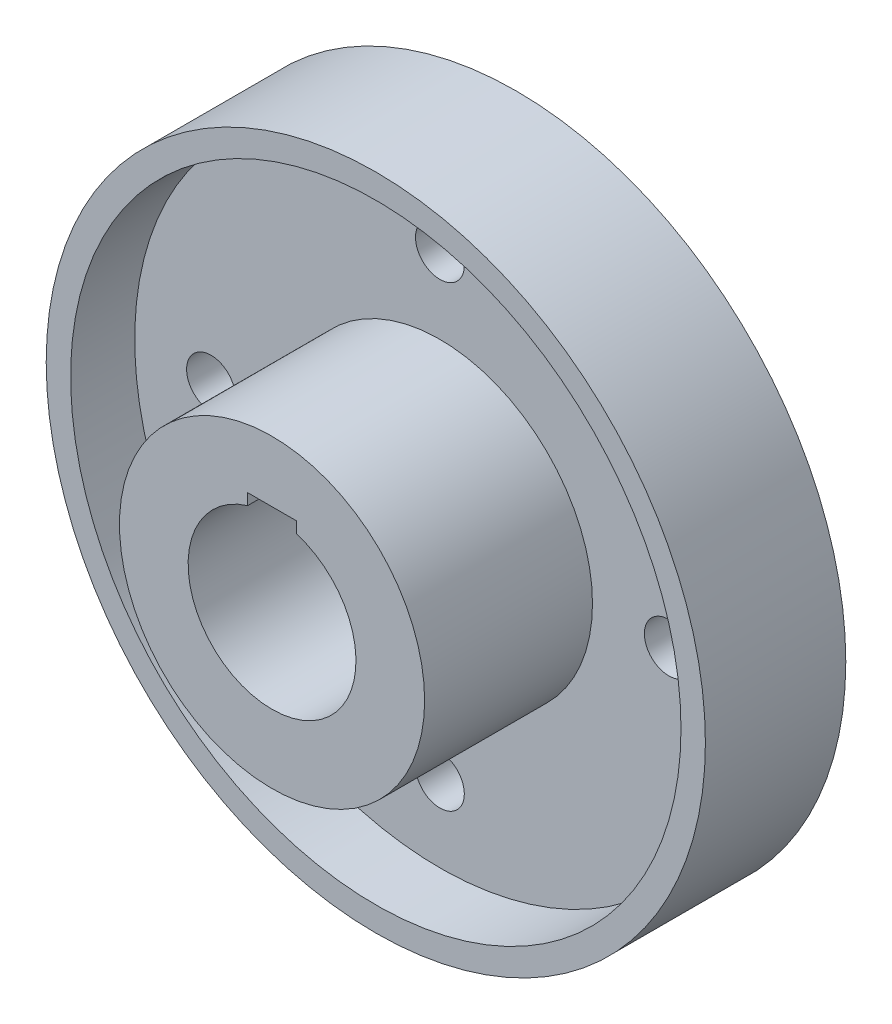
SolidWorks part; units mm, degrees
material "Gray Cast Iron"
ref_plane "Front Plane" through (0, 0, 0) normal (0, 0, 1) x (1, 0, 0)
ref_plane "Top Plane" through (0, 0, 0) normal (0, 1, 0) x (1, 0, 0)
ref_plane "Right Plane" through (0, 0, 0) normal (1, 0, 0) x (0, 0, -1)
sketch "Sketch1" plane through (0, 0, 0) normal (0, 0, 1) x (1, 0, 0)
  circle A0 centre (0, 0) radius 108
  dimension "D1" = 216
extrude "Boss-Extrude1" add sketch "Sketch1" along normal blind 25 contours A0
sketch "Sketch2" plane through (0, 0, 25) normal (0, 0, 1) x (1, 0, 0)
  circle A0 centre (0, 0) radius 108
  circle A1 centre (0, 0) radius 100
  dimension "D1" = 216
  dimension "D2" = 200
extrude "Boss-Extrude2" add sketch "Sketch2" along normal blind 21
sketch "Sketch3" plane through (0, 0, 25) normal (0, 0, 1) x (1, 0, 0)
  circle A0 centre (0, 0) radius 50
  circle A1 centre (0, 0) radius 27.5
  dimension "D1" = 100
  dimension "D2" = 55
extrude "Boss-Extrude3" add sketch "Sketch3" along normal blind 55
sketch "Sketch4" plane through (0, 0, 0) normal (0, 0, -1) x (-1, 0, 0)
  circle A0 centre (0, 0) radius 37.5
  dimension "D1" = 75
extrude "Boss-Extrude4" add sketch "Sketch4" along normal blind 5
sketch "Sketch6" plane through (0, 0, 25) normal (0, 0, 1) x (1, 0, 0)
  circle A0 centre (0, 0) radius 27.5
  dimension "D1" = 55
extrude "Cut-Extrude1" cut sketch "Sketch6" against normal through all
sketch "Sketch7" plane through (0, 0, 25) normal (0, 0, 1) x (1, 0, 0)
  line L0 (0, 0) -> (0, 75) construction
  circle A0 centre (0, 0) radius 75 construction
  circle A1 centre (0, 75) radius 8
  circle A2 centre (75, 0) radius 8
  circle A3 centre (0, -75) radius 8
  circle A4 centre (-75, 0) radius 8
  circle A5 centre (0, 0) radius 50 construction
  point P14 (0, 0)
  dimension "D1" = 150
  dimension "D2" = 16
  dimension "D4" = 75
  dimension "D3" = 4
extrude "Cut-Extrude2" cut sketch "Sketch7" against normal through all
sketch "Sketch9" plane through (0, 0, 80) normal (0, 0, 1) x (1, 0, 0)
  line L0 (0, 30) -> (0, 0) construction
  line L1 (-8, 30) -> (8, 30)
  line L2 (-8, 30) -> (-8, 0)
  line L3 (-8, 0) -> (8, 0)
  line L4 (8, 0) -> (8, 30)
  circle A3 centre (0, 0) radius 50 construction
  point P8 (0, 30)
  dimension "D1" = 30
  dimension "D3" = 16
extrude "Cut-Extrude4" cut sketch "Sketch9" against normal through all contours L1 L4 L3 L2
